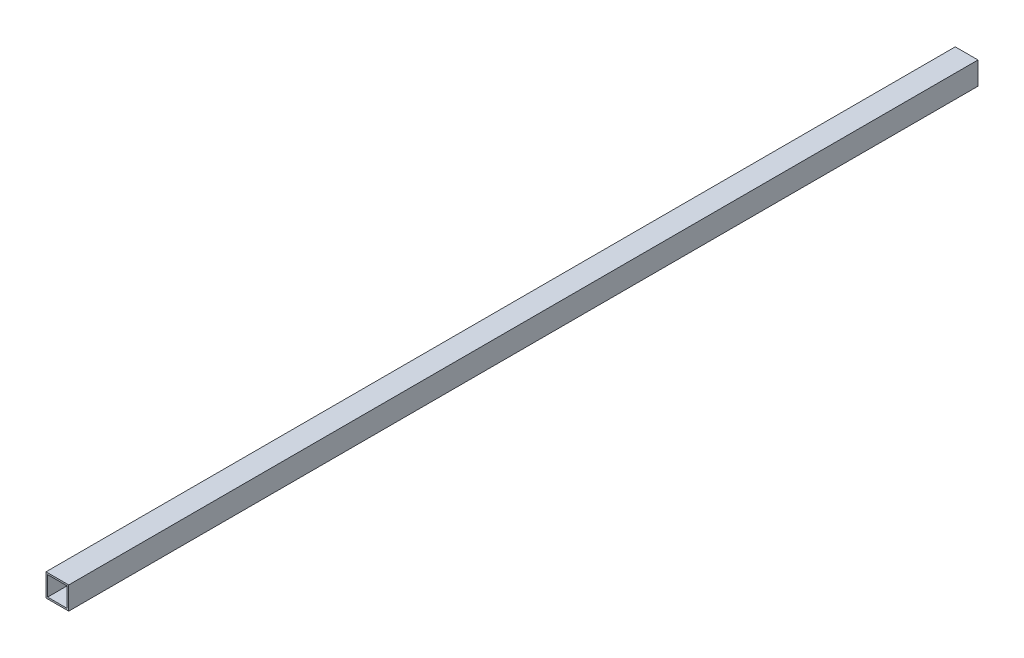
SolidWorks part; units mm, degrees
material "6063-T6"
ref_plane "Front Plane" through (0, 0, 0) normal (0, 0, 1) x (1, 0, 0)
ref_plane "Top Plane" through (0, 0, 0) normal (0, 1, 0) x (1, 0, 0)
ref_plane "Right Plane" through (0, 0, 0) normal (1, 0, 0) x (0, 0, -1)
sketch "Sketch1" plane through (0, 0, 0) normal (0, 0, 1) x (1, 0, 0)
  line L0 (3.175, 41.275) -> (41.275, 41.275)
  line L1 (0, 0) -> (44.45, 0)
  line L2 (0, 0) -> (0, 44.45)
  line L3 (0, 44.45) -> (44.45, 44.45)
  line L4 (44.45, 0) -> (44.45, 44.45)
  line L5 (41.275, 3.175) -> (41.275, 41.275)
  line L6 (3.175, 3.175) -> (41.275, 3.175)
  line L7 (3.175, 3.175) -> (3.175, 41.275)
  dimension "D1" = 3.175
  dimension "D2" = 44.45
extrude "Boss-Extrude1" add sketch "Sketch1" along normal blind 1778
